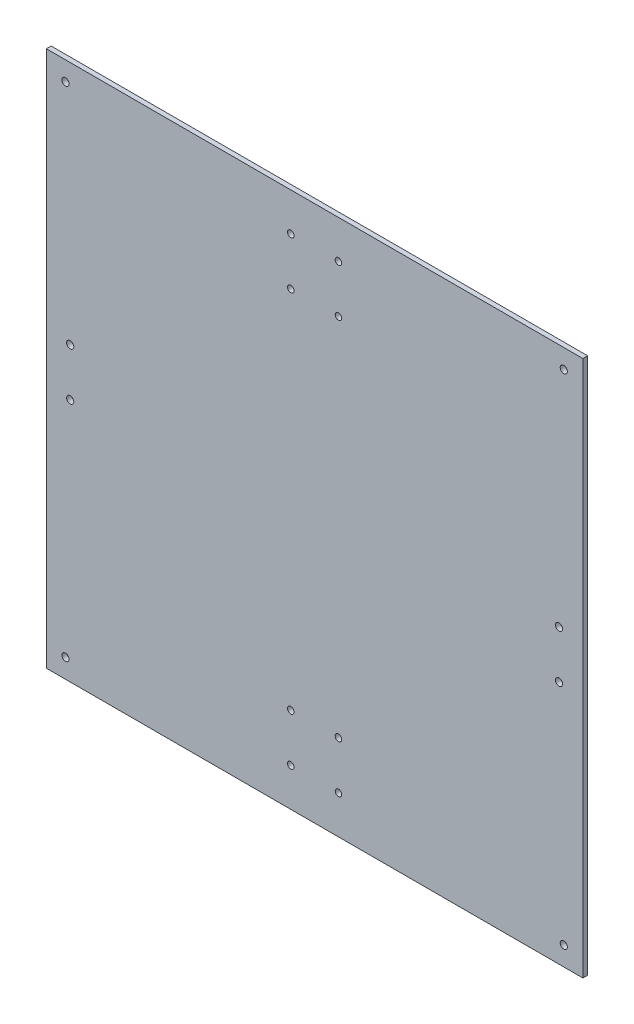
SolidWorks part; units mm, degrees
ref_plane "Front Plane" through (0, 0, 0) normal (0, 0, 1) x (1, 0, 0)
ref_plane "Top Plane" through (0, 0, 0) normal (0, 1, 0) x (1, 0, 0)
ref_plane "Right Plane" through (0, 0, 0) normal (1, 0, 0) x (0, 0, -1)
sketch "Sketch1" plane through (0, 0, 0) normal (0, 0, 1) x (1, 0, 0)
  line L0 (21, -186.5) -> (16, -186.5) construction
  line L1 (112.5, 26) -> (-112.5, 26)
  line L2 (112.5, 26) -> (112.5, -199)
  line L3 (112.5, -199) -> (-112.5, -199)
  line L4 (-112.5, 26) -> (-112.5, -199)
  line L5 (-16, -13) -> (-16, 13) construction
  line L7 (16, 13) -> (16, -13) construction
  line L9 (-16, 13.5) -> (16, 13.5) construction
  line L10 (0, 26) -> (0, -199) construction
  line L12 (104.5, 18) -> (-104.5, 18)
  line L13 (104.5, 18) -> (104.5, -191)
  line L14 (104.5, -191) -> (-104.5, -191)
  line L15 (-104.5, 18) -> (-104.5, -191)
  circle A0 centre (10, -10) radius 1.35
  circle A1 centre (-10, -10) radius 1.375
  circle A2 centre (-10, 10) radius 1.375
  circle A3 centre (10, 10) radius 1.375
  circle A4 centre (10, -183) radius 1.35
  circle A5 centre (-10, -183) radius 1.375
  circle A6 centre (-10, -163) radius 1.375
  circle A7 centre (10, -163) radius 1.375
  circle A8 centre (102.5, -76.5) radius 1.5
  circle A9 centre (102.5, -96.5) radius 1.5
  circle A10 centre (-102.5, -76.5) radius 1.5
  circle A11 centre (-102.5, -96.5) radius 1.5
  circle A12 centre (104.5, 18) radius 1.5
  circle A13 centre (104.5, -191) radius 1.5
  circle A14 centre (-104.5, -191) radius 1.5
  circle A15 centre (-104.5, 18) radius 1.5
  dimension "D7" = 3
  dimension "D8" = 3
  dimension "D9" = 20
  dimension "D11" = 10
  dimension "D12" = 10
  dimension "D13" = 3
  dimension "D14" = 3
  dimension "D15" = 3
  dimension "D16" = 3
  dimension "D1" = 225
  dimension "D2" = 225
  dimension "D3" = 12.5
  dimension "D4" = 96.5
  dimension "D5" = 96.5
  dimension "D6" = 12.5
  dimension "D10" = 102.5
  dimension "D17" = 209
  dimension "D18" = 209
  dimension "D19" = 8
  dimension "D20" = 8
  dimension "D21" = 8
  dimension "D22" = 8
extrude "Boss-Extrude1" add sketch "Sketch1" along normal blind 2 contours L10 L12 A15 L15 A14 L14 A10 A6 A5 A2 A1 A11 | L10 L1 L4 L3 L14 A14 L15 A15 L12 | L12 L10 L14 A13 L13 A12 A0 A3 A4 A7 A8 A9 | L1 L10 L12 A12 L13 A13 L14 L3 L2
